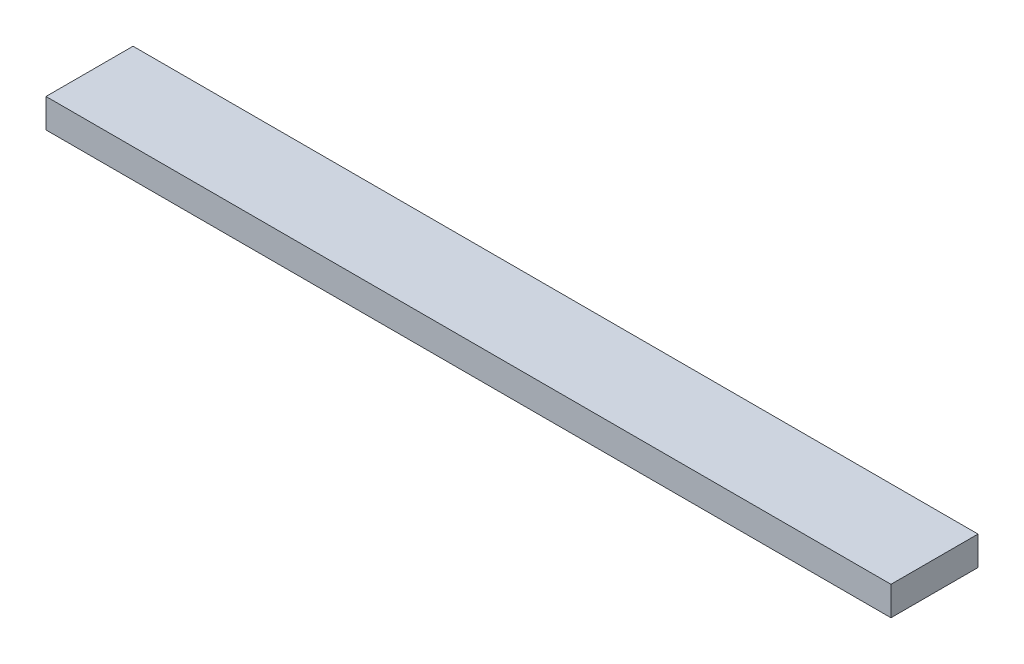
SolidWorks part; units mm, degrees
ref_plane "Спереди" through (0, 0, 0) normal (0, 0, 1) x (1, 0, 0)
ref_plane "Сверху" through (0, 0, 0) normal (0, 1, 0) x (1, 0, 0)
ref_plane "Справа" through (0, 0, 0) normal (1, 0, 0) x (0, 0, -1)
sketch "Эскиз1" plane through (0, 0, 0) normal (0, 1, 0) x (1, 0, 0)
  line L1 (-291.2541, 30) -> (291.2541, 30)
  line L2 (-291.2541, 30) -> (-291.2541, -30)
  line L3 (-291.2541, -30) -> (291.2541, -30)
  line L4 (291.2541, 30) -> (291.2541, -30)
  line L5 (-291.2541, 30) -> (291.2541, -30) construction
  line L6 (-291.2541, -30) -> (291.2541, 30) construction
  point P0 (0, 0)
extrude "Бобышка-Вытянуть1" add sketch "Эскиз1" along normal blind 20
